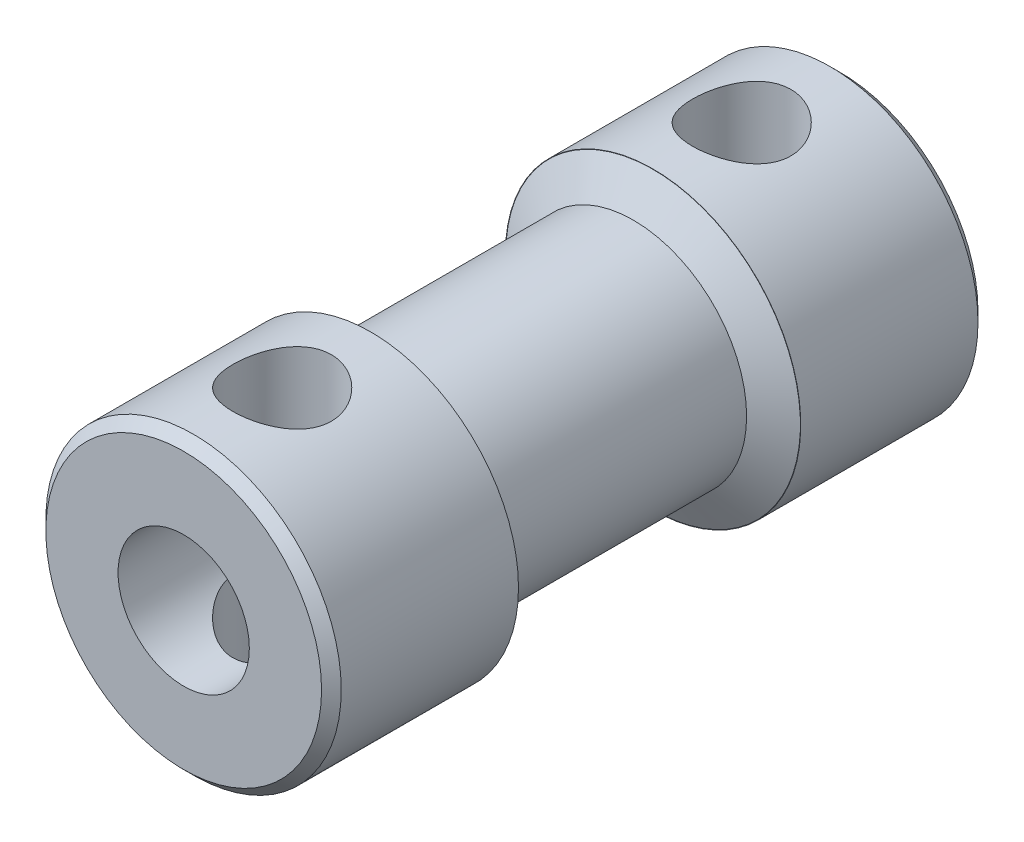
SolidWorks part; units mm, degrees
ref_plane "Horní rovina" through (0, 0, 0) normal (0, 0, 1) x (1, 0, 0)
ref_plane "Přední rovina" through (0, 0, 0) normal (0, 1, 0) x (1, 0, 0)
ref_plane "Pravá rovina" through (0, 0, 0) normal (1, 0, 0) x (0, 0, -1)
ref_plane "Rovina1" through (0, 0, 30) normal (0, 0, 1) x (1, 0, 0)
sketch "Skica8" plane through (23.8, 0, 0) normal (0, 0, 1) x (1, 0, 0)
  circle A3 centre (-23.8, 0) radius 1.5
  circle A4 centre (-23.8, 0) radius 4.5
  dimension "D1" = 3
  dimension "D2" = 9
extrude "Přidat vysunutím8" add sketch "Skica8" along normal blind 20
sketch "Skica9" plane through (0, 0, 0) normal (1, 0, 0) x (0, 0, -1)
  line L0 (0, 0) -> (-54.894, 0) construction
  line L5 (-10, 0) -> (-10, 7.7363) construction
  line L6 (-14.3, 5.3345) -> (-5.7, 5.3345)
  line L7 (-14.3, 3.45) -> (-5.7, 3.45)
  line L8 (-5.7, 5.3345) -> (-5.7, 3.45)
  line L9 (-14.3, 5.3345) -> (-14.3, 3.45)
  point P11 (-10, 5.3345)
  dimension "D1" = 10
  dimension "D2" = 8.6
revolve "Odebrat rotací1" cut sketch "Skica9" angle 360 about L0
chamfer "Zkosení1" distance 0.6 angle 60 1 edges at (-3.45, 0, 5.7)
chamfer "Zkosení2" distance 0.6 angle 60 1 edges at (-3.45, 0, 14.3)
chamfer "Zkosení3" distance 0.3 angle 45 2 edges at (4.5, 0, 0) (4.5, 0, 20)
sketch "Skica10" plane through (0, 0, 0) normal (0, 1, 0) x (1, 0, 0)
  line L0 (0, 0) -> (0, -20.789) construction
  line L1 (4.2, 0) -> (-4.2, 0) construction
  line L2 (-4.2, -20) -> (4.2, -20) construction
  circle A0 centre (0, -3) radius 1.5
  circle A1 centre (0, -17) radius 1.5
  dimension "D1" = 3
  dimension "D2" = 3
  dimension "D3" = 3
  dimension "D4" = 3
extrude "Odebrat vysunutím1" cut sketch "Skica10" against normal mid plane 20
sketch "Skica11" plane through (0, 0, 20) normal (0, 0, 1) x (1, 0, 0)
  circle A0 centre (0, 0) radius 2
  dimension "D1" = 4
extrude "Odebrat vysunutím2" cut sketch "Skica11" against normal blind 10
